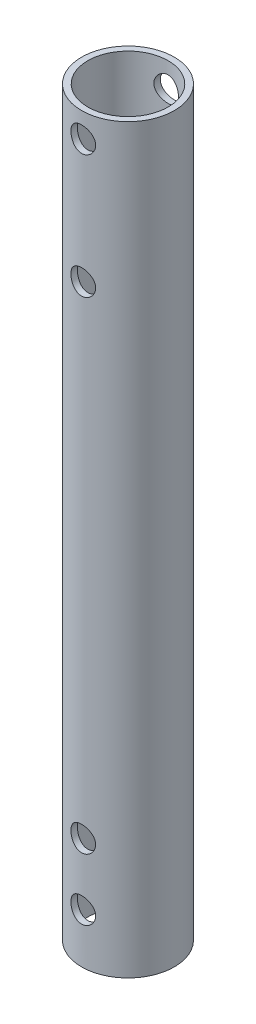
SolidWorks part; units mm, degrees
material "Carbon Fibre"
ref_plane "Front Plane" through (0, 0, 0) normal (0, 0, 1) x (1, 0, 0)
ref_plane "Top Plane" through (0, 0, 0) normal (0, 1, 0) x (1, 0, 0)
ref_plane "Right Plane" through (0, 0, 0) normal (1, 0, 0) x (0, 0, -1)
sketch "Sketch1" plane through (0, 0, 0) normal (0, 1, 0) x (1, 0, 0)
  circle A0 centre (0, 0) radius 6.5
  circle A1 centre (0, 0) radius 7.5
  dimension "D1" = 15
  dimension "D2" = 13
extrude "Boss-Extrude1" add sketch "Sketch1" along normal blind 120
sketch "Sketch3" plane through (0, 0, 0) normal (0, 0, -1) x (-1, 0, 0)
  line L0 (-7.5, 0) -> (7.5, 0) construction
  line L1 (7.5, 120) -> (-7.5, 120) construction
  circle A0 centre (0, 116) radius 2
  circle A1 centre (0, 96) radius 2
  circle A2 centre (0, 8) radius 2
  circle A3 centre (0, 18) radius 2
  dimension "D1" = 4
  dimension "D4" = 4
  dimension "D6" = 10
  dimension "D2" = 4
  dimension "D3" = 20
  dimension "D5" = 8
extrude "Cut-Extrude1" cut sketch "Sketch3" against normal through all both and the other way through all contours A0
equation "\"D1@Boss-Extrude1\"= 0.6*200.00mm"
